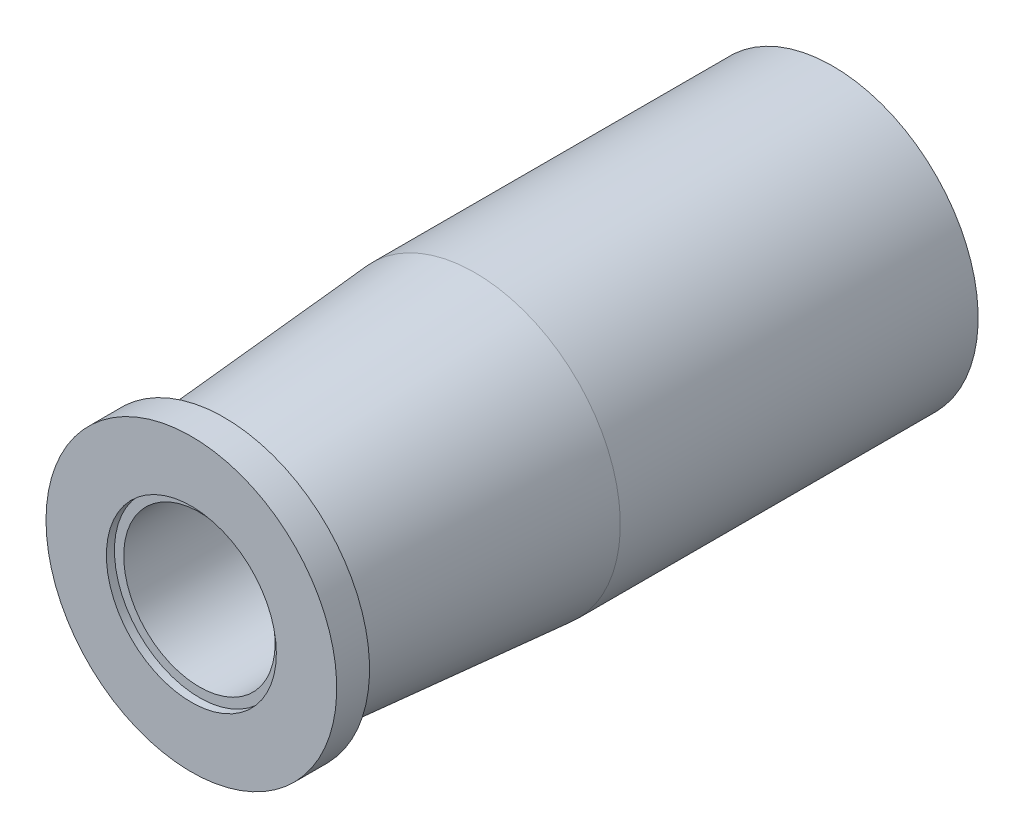
SolidWorks part; units mm, degrees
ref_plane "Front Plane" through (0, 0, 0) normal (0, 0, 1) x (1, 0, 0)
ref_plane "Top Plane" through (0, 0, 0) normal (0, 1, 0) x (1, 0, 0)
ref_plane "Right Plane" through (0, 0, 0) normal (1, 0, 0) x (0, 0, -1)
sketch "Sketch1" plane through (0, 0, 0) normal (0, 1, 0) x (1, 0, 0)
  line L0 (0, 0) -> (-4.875, 0)
  line L1 (-4.875, 0) -> (-4.875, 1.1)
  line L2 (-4.875, 1.1) -> (-4.215, 1.1)
  line L3 (-4.215, 1.1) -> (-4.875, 9.51)
  line L4 (-4.875, 9.51) -> (-4.875, 21.51)
  line L5 (-4.875, 21.51) -> (0, 21.51)
  line L6 (0, 21.51) -> (0, 0)
  dimension "D1" = 4.875
  dimension "D2" = 4.875
  dimension "D3" = 1.1
  dimension "D4" = 4.215
  dimension "D5" = 12
  dimension "D6" = 21.51
revolve "Revolve1" add sketch "Sketch1" angle 360 about L6
sketch "Sketch2" plane through (0, 0, 0) normal (0, 0, 1) x (1, 0, 0)
  circle A0 centre (0, 0) radius 2.85
  dimension "D1" = 5.7
extrude "Cut-Extrude1" cut sketch "Sketch2" against normal blind 0.27
sketch "Sketch3" plane through (0, 0, -0.27) normal (0, 0, 1) x (1, 0, 0)
  circle A0 centre (0, 0) radius 2.5391
extrude "Cut-Extrude2" cut sketch "Sketch3" against normal blind 5
sketch "Sketch4" plane through (0, 0, -21.51) normal (0, 0, -1) x (-1, 0, 0)
  circle A0 centre (0, 0) radius 1.5
  dimension "D1" = 3
extrude "Cut-Extrude3" cut sketch "Sketch4" against normal blind 19
